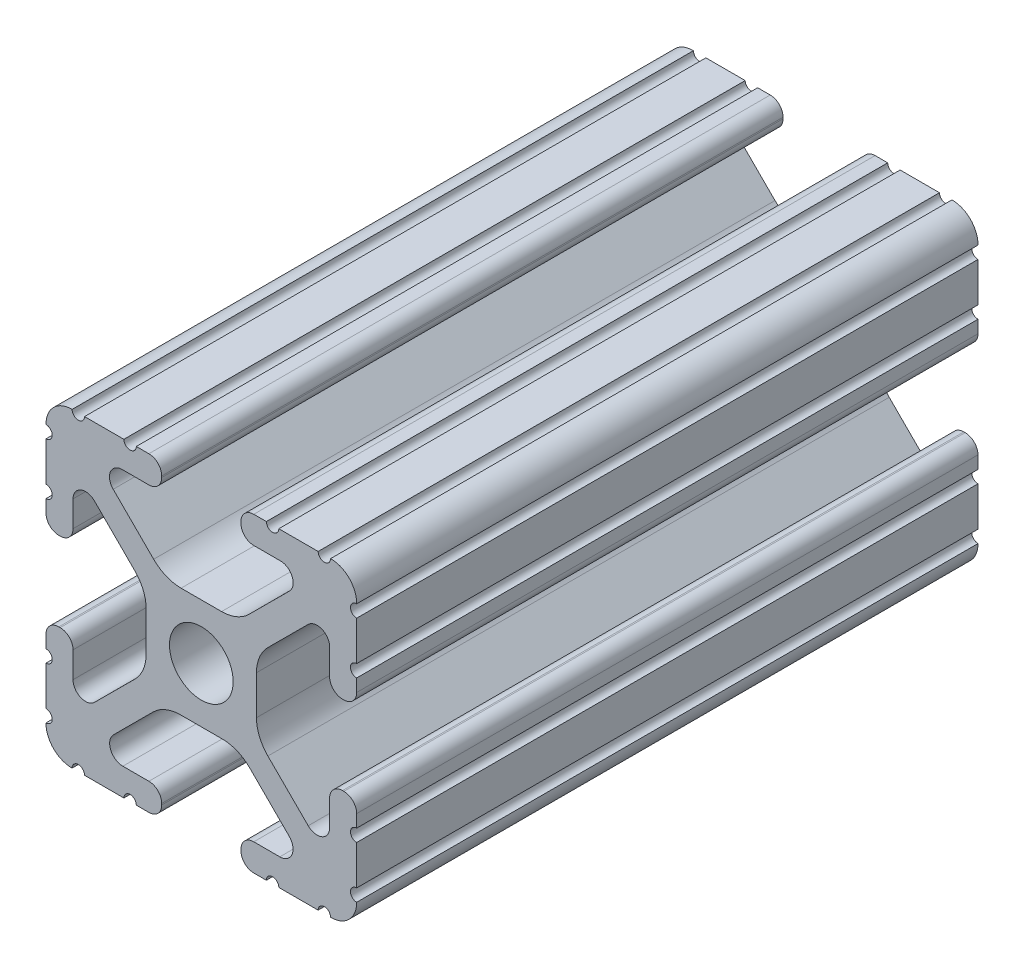
SolidWorks part; units mm, degrees
ref_plane "Front Plane" through (0, 0, 0) normal (0, 0, 1) x (1, 0, 0)
ref_plane "Top Plane" through (0, 0, 0) normal (0, 1, 0) x (1, 0, 0)
ref_plane "Right Plane" through (0, 0, 0) normal (1, 0, 0) x (0, 0, -1)
sketch "Sketch1" plane through (0, 0, 0) normal (0, 0, 1) x (1, 0, 0)
  line L88 (-7.1797, -8.6452) -> (-3.9523, -5.4237)
  line L89 (-1.7093, -4.4958) -> (1.7093, -4.4958)
  line L90 (3.9523, -5.4237) -> (7.1797, -8.6452)
  line L91 (6.4164, -10.4902) -> (4.2875, -10.4902)
  line L92 (3.2385, -11.5392) -> (3.2385, -11.651)
  line L93 (4.2875, -12.7) -> (5.3171, -12.7)
  line L94 (6.3331, -12.7) -> (9.5504, -12.7)
  line L95 (12.7, -9.5504) -> (12.7, -6.3331)
  line L96 (12.7, -5.3171) -> (12.7, -4.2875)
  line L97 (11.651, -3.2385) -> (11.5392, -3.2385)
  line L98 (10.4902, -4.2875) -> (10.4902, -6.4021)
  line L99 (8.7371, -7.1294) -> (5.441, -3.8408)
  line L100 (4.5085, -1.5932) -> (4.5085, 1.5932)
  line L101 (5.441, 3.8408) -> (8.7371, 7.1294)
  line L102 (10.4902, 6.4021) -> (10.4902, 4.2875)
  line L103 (11.5392, 3.2385) -> (11.651, 3.2385)
  line L104 (12.7, 4.2875) -> (12.7, 5.3171)
  line L105 (12.7, 6.3331) -> (12.7, 9.5504)
  line L106 (9.5504, 12.7) -> (6.3331, 12.7)
  line L107 (5.3171, 12.7) -> (4.2875, 12.7)
  line L108 (3.2385, 11.651) -> (3.2385, 11.5392)
  line L109 (4.2875, 10.4902) -> (6.4768, 10.4902)
  line L110 (7.207, 8.7244) -> (3.8983, 5.4232)
  line L111 (1.6558, 4.4958) -> (-1.6558, 4.4958)
  line L112 (-3.8983, 5.4232) -> (-7.207, 8.7244)
  line L113 (-6.4768, 10.4902) -> (-4.2875, 10.4902)
  line L114 (-3.2385, 11.5392) -> (-3.2385, 11.651)
  line L115 (-4.2875, 12.7) -> (-5.3171, 12.7)
  line L116 (-6.3331, 12.7) -> (-9.5504, 12.7)
  line L117 (-12.7, 9.5504) -> (-12.7, 6.3331)
  line L118 (-12.7, 5.3171) -> (-12.7, 4.2875)
  line L119 (-11.651, 3.2385) -> (-11.5392, 3.2385)
  line L120 (-10.4902, 4.2875) -> (-10.4902, 6.4021)
  line L121 (-8.7371, 7.1294) -> (-5.441, 3.8408)
  line L122 (-4.5085, 1.5932) -> (-4.5085, -1.5932)
  line L123 (-5.441, -3.8408) -> (-8.7371, -7.1294)
  line L124 (-10.4902, -6.4021) -> (-10.4902, -4.2875)
  line L125 (-11.5392, -3.2385) -> (-11.651, -3.2385)
  line L126 (-12.7, -4.2875) -> (-12.7, -5.3171)
  line L127 (-12.7, -6.3331) -> (-12.7, -9.5504)
  line L128 (-9.5504, -12.7) -> (-6.3331, -12.7)
  line L129 (-5.3171, -12.7) -> (-4.2875, -12.7)
  line L130 (-3.2385, -11.651) -> (-3.2385, -11.5392)
  line L131 (-4.2875, -10.4902) -> (-6.4164, -10.4902)
  circle A1 centre (0, 0) radius 2.6035
  arc A104 (-7.1797, -8.6452) -> (-6.4164, -10.4902) centre (-6.4164, -9.4098) ccw
  arc A105 (-1.7093, -4.4958) -> (-3.9523, -5.4237) centre (-1.7093, -7.6708) ccw
  arc A106 (3.9523, -5.4237) -> (1.7093, -4.4958) centre (1.7093, -7.6708) ccw
  arc A107 (6.4164, -10.4902) -> (7.1797, -8.6452) centre (6.4164, -9.4098) ccw
  arc A108 (4.2875, -10.4902) -> (3.2385, -11.5392) centre (4.2875, -11.5392) ccw
  arc A109 (3.2385, -11.651) -> (4.2875, -12.7) centre (4.2875, -11.651) ccw
  arc A110 (6.3331, -12.7) -> (5.3171, -12.7) centre (5.8251, -12.7) ccw
  arc A111 (10.5664, -12.6998) -> (9.5504, -12.7) centre (10.0584, -12.7) ccw
  arc A112 (10.5664, -12.6998) -> (12.6998, -10.5664) centre (10.5918, -10.5918) ccw
  arc A113 (12.7, -9.5504) -> (12.6998, -10.5664) centre (12.7, -10.0584) ccw
  arc A114 (12.7, -5.3171) -> (12.7, -6.3331) centre (12.7, -5.8251) ccw
  arc A115 (12.7, -4.2875) -> (11.651, -3.2385) centre (11.651, -4.2875) ccw
  arc A116 (11.5392, -3.2385) -> (10.4902, -4.2875) centre (11.5392, -4.2875) ccw
  arc A117 (8.7371, -7.1294) -> (10.4902, -6.4021) centre (9.4628, -6.4021) ccw
  arc A118 (4.5085, -1.5932) -> (5.441, -3.8408) centre (7.6835, -1.5932) ccw
  arc A119 (5.441, 3.8408) -> (4.5085, 1.5932) centre (7.6835, 1.5932) ccw
  arc A120 (10.4902, 6.4021) -> (8.7371, 7.1294) centre (9.4628, 6.4021) ccw
  arc A121 (10.4902, 4.2875) -> (11.5392, 3.2385) centre (11.5392, 4.2875) ccw
  arc A122 (11.651, 3.2385) -> (12.7, 4.2875) centre (11.651, 4.2875) ccw
  arc A123 (12.7, 6.3331) -> (12.7, 5.3171) centre (12.7, 5.8251) ccw
  arc A124 (12.6998, 10.5664) -> (12.7, 9.5504) centre (12.7, 10.0584) ccw
  arc A125 (12.6998, 10.5664) -> (10.5664, 12.6998) centre (10.5918, 10.5918) ccw
  arc A126 (9.5504, 12.7) -> (10.5664, 12.6998) centre (10.0584, 12.7) ccw
  arc A127 (5.3171, 12.7) -> (6.3331, 12.7) centre (5.8251, 12.7) ccw
  arc A128 (4.2875, 12.7) -> (3.2385, 11.651) centre (4.2875, 11.651) ccw
  arc A129 (3.2385, 11.5392) -> (4.2875, 10.4902) centre (4.2875, 11.5392) ccw
  arc A130 (7.207, 8.7244) -> (6.4768, 10.4902) centre (6.4768, 9.4563) ccw
  arc A131 (1.6558, 4.4958) -> (3.8983, 5.4232) centre (1.6558, 7.6708) ccw
  arc A132 (-3.8983, 5.4232) -> (-1.6558, 4.4958) centre (-1.6558, 7.6708) ccw
  arc A133 (-6.4768, 10.4902) -> (-7.207, 8.7244) centre (-6.4768, 9.4563) ccw
  arc A134 (-4.2875, 10.4902) -> (-3.2385, 11.5392) centre (-4.2875, 11.5392) ccw
  arc A135 (-3.2385, 11.651) -> (-4.2875, 12.7) centre (-4.2875, 11.651) ccw
  arc A136 (-6.3331, 12.7) -> (-5.3171, 12.7) centre (-5.8251, 12.7) ccw
  arc A137 (-10.5664, 12.6998) -> (-9.5504, 12.7) centre (-10.0584, 12.7) ccw
  arc A138 (-10.5664, 12.6998) -> (-12.6998, 10.5664) centre (-10.5918, 10.5918) ccw
  arc A139 (-12.7, 9.5504) -> (-12.6998, 10.5664) centre (-12.7, 10.0584) ccw
  arc A140 (-12.7, 5.3171) -> (-12.7, 6.3331) centre (-12.7, 5.8251) ccw
  arc A141 (-12.7, 4.2875) -> (-11.651, 3.2385) centre (-11.651, 4.2875) ccw
  arc A142 (-11.5392, 3.2385) -> (-10.4902, 4.2875) centre (-11.5392, 4.2875) ccw
  arc A143 (-8.7371, 7.1294) -> (-10.4902, 6.4021) centre (-9.4628, 6.4021) ccw
  arc A144 (-4.5085, 1.5932) -> (-5.441, 3.8408) centre (-7.6835, 1.5932) ccw
  arc A145 (-5.441, -3.8408) -> (-4.5085, -1.5932) centre (-7.6835, -1.5932) ccw
  arc A146 (-10.4902, -6.4021) -> (-8.7371, -7.1294) centre (-9.4628, -6.4021) ccw
  arc A147 (-10.4902, -4.2875) -> (-11.5392, -3.2385) centre (-11.5392, -4.2875) ccw
  arc A148 (-11.651, -3.2385) -> (-12.7, -4.2875) centre (-11.651, -4.2875) ccw
  arc A149 (-12.7, -6.3331) -> (-12.7, -5.3171) centre (-12.7, -5.8251) ccw
  arc A150 (-12.6998, -10.5664) -> (-12.7, -9.5504) centre (-12.7, -10.0584) ccw
  arc A151 (-12.6998, -10.5664) -> (-10.5664, -12.6998) centre (-10.5918, -10.5918) ccw
  arc A152 (-9.5504, -12.7) -> (-10.5664, -12.6998) centre (-10.0584, -12.7) ccw
  arc A153 (-5.3171, -12.7) -> (-6.3331, -12.7) centre (-5.8251, -12.7) ccw
  arc A154 (-4.2875, -12.7) -> (-3.2385, -11.651) centre (-4.2875, -11.651) ccw
  arc A155 (-3.2385, -11.5392) -> (-4.2875, -10.4902) centre (-4.2875, -11.5392) ccw
extrude "Boss-Extrude1" add sketch "Sketch1" along normal mid plane 50.8
sketch "Sketch2" plane through (0, 0, 0) normal (0, 1, 0) x (1, 0, 0)
  line L0 (0, 25.4) -> (0, -25.4) construction
  line L1 (1.6558, 25.4) -> (-1.6558, 25.4) construction
  line L2 (1.6558, -25.4) -> (-1.6558, -25.4) construction
  circle A0 centre (0, 12.7) radius 3.175
  circle A1 centre (0, -15.875) radius 3.175
  dimension "D1" = 6.35
  dimension "D2" = 12.7
  dimension "D3" = 9.525
extrude "Cut-Extrude1" cut sketch "Sketch2" against normal through all both and the other way through all contours A0 L0 | L0 A0 | A1 L0 | L0 A1
